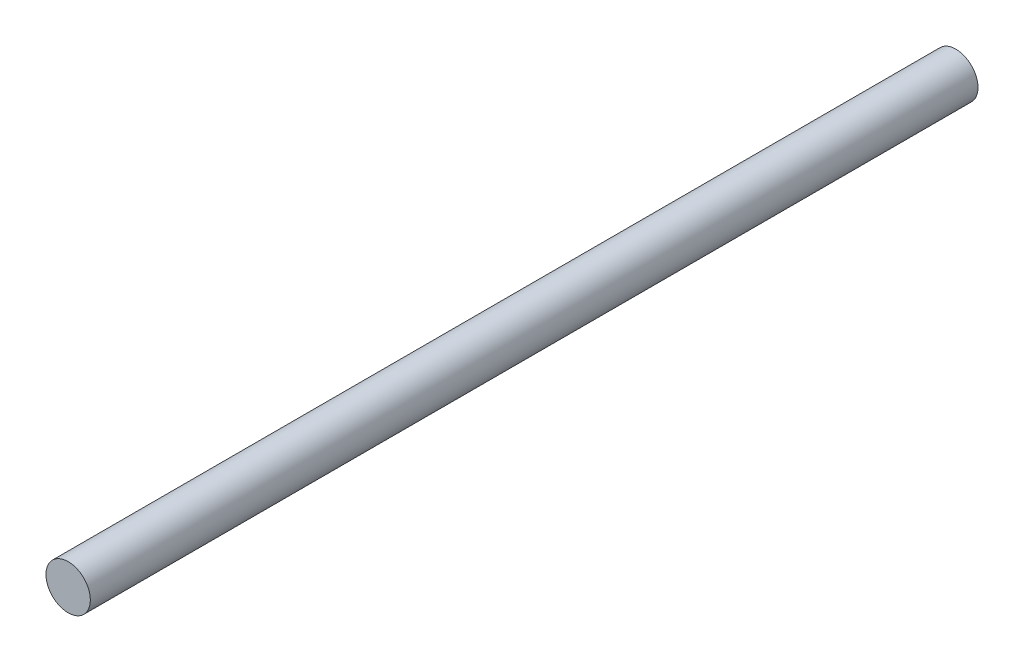
SolidWorks part; units mm, degrees
ref_plane "Alzado" through (0, 0, 0) normal (0, 0, 1) x (1, 0, 0)
ref_plane "Planta" through (0, 0, 0) normal (0, 1, 0) x (1, 0, 0)
ref_plane "Vista lateral" through (0, 0, 0) normal (1, 0, 0) x (0, 0, -1)
sketch "Croquis1" plane through (0, 0, 0) normal (0, 0, 1) x (1, 0, 0)
  circle A0 centre (0, 0) radius 6
  dimension "D1" = 12
extrude "Saliente-Extruir1" add sketch "Croquis1" along normal blind 240
